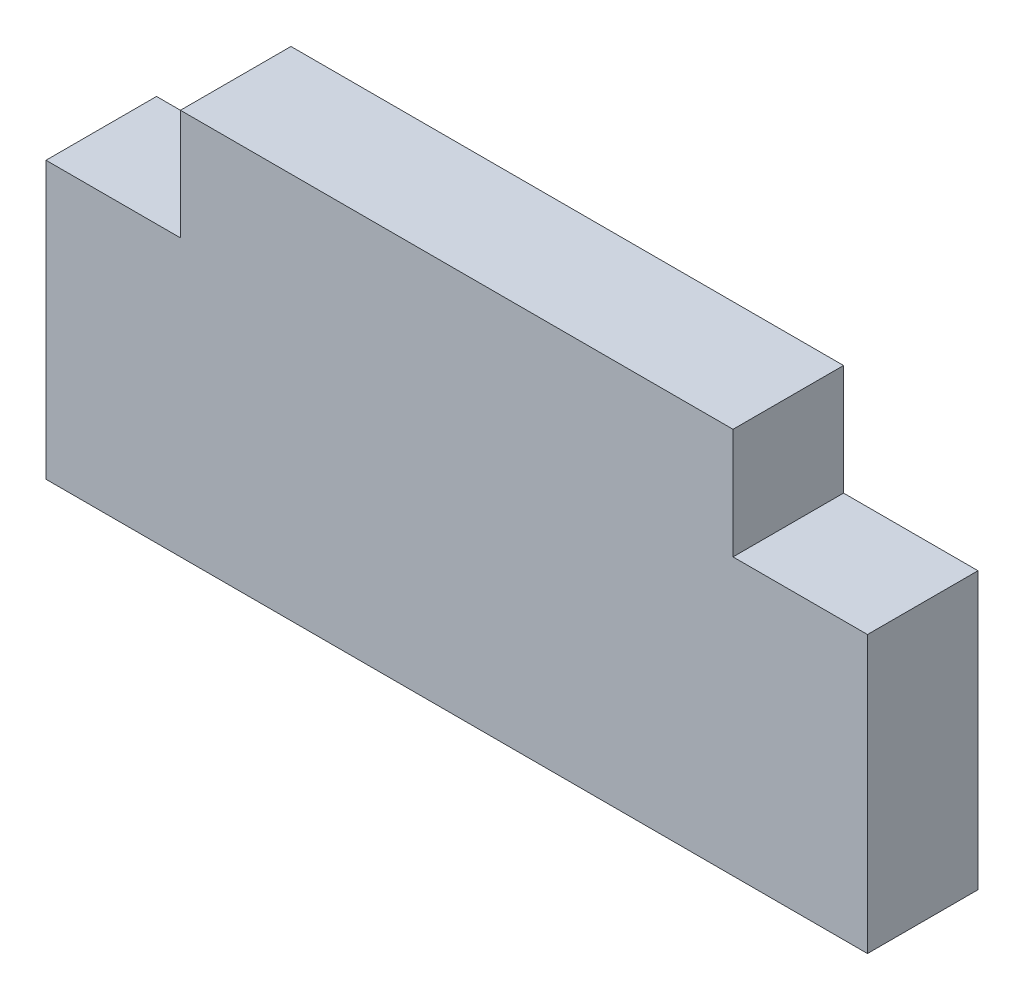
SolidWorks part; units mm, degrees
ref_plane "Front Plane" through (0, 0, 0) normal (0, 0, 1) x (1, 0, 0)
ref_plane "Top Plane" through (0, 0, 0) normal (0, 1, 0) x (1, 0, 0)
ref_plane "Right Plane" through (0, 0, 0) normal (1, 0, 0) x (0, 0, -1)
sketch "Sketch1" plane through (0, 0, 0) normal (0, 1, 0) x (1, 0, 0)
  line L1 (-7.433, 1) -> (7.433, 1)
  line L2 (-7.433, 1) -> (-7.433, -1)
  line L3 (-7.433, -1) -> (7.433, -1)
  line L4 (7.433, 1) -> (7.433, -1)
  circle A0 centre (0, 0) radius 7.5 construction
  dimension "D1" = 15
  dimension "D2" = 2
extrude "Boss-Extrude1" add sketch "Sketch1" along normal blind 5
sketch "Sketch2" plane through (0, 5, 0) normal (0, 1, 0) x (1, 0, 0)
  line L0 (-7.433, -1) -> (7.433, -1) construction
  line L1 (-5, -1) -> (5, -1)
  line L2 (-5, -1) -> (-5, 1)
  line L3 (-5, 1) -> (5, 1)
  line L4 (5, -1) -> (5, 1)
  line L5 (7.433, 1) -> (-7.433, 1) construction
  dimension "D1" = 10
  dimension "D2" = 5
extrude "Boss-Extrude2" add sketch "Sketch2" along normal blind 2
